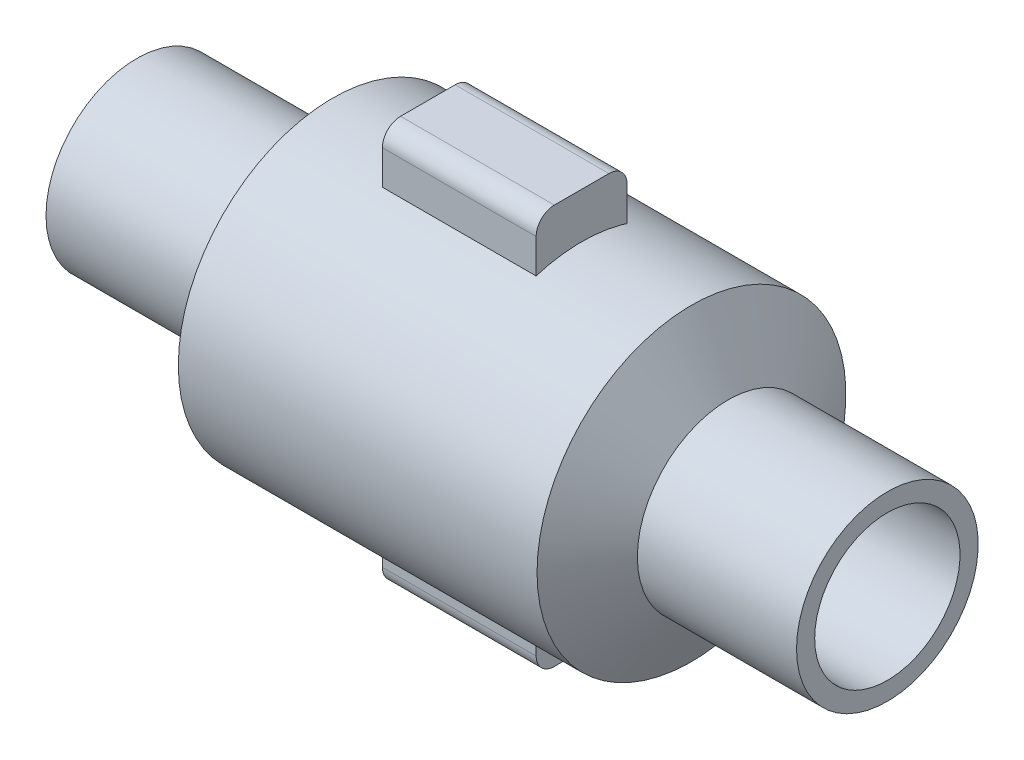
SolidWorks part; units mm, degrees
ref_plane "Front Plane" through (0, 0, 0) normal (0, 0, 1) x (1, 0, 0)
ref_plane "Top Plane" through (0, 0, 0) normal (0, 1, 0) x (1, 0, 0)
ref_plane "Right Plane" through (0, 0, 0) normal (1, 0, 0) x (0, 0, -1)
sketch "Sketch1" plane through (0, 0, 0) normal (0, 0, 1) x (1, 0, 0)
  line L0 (0, 160) -> (0, 200)
  line L1 (0, 200) -> (350.52, 200)
  line L2 (350.52, 200) -> (431.349, 340)
  line L3 (431.349, 340) -> (1221.289, 340)
  line L4 (1221.289, 340) -> (1302.1181, 200)
  line L5 (1302.1181, 200) -> (1652.6381, 200)
  line L6 (1652.6381, 200) -> (1652.6381, 160)
  line L8 (39.8559, 160) -> (350.52, 160)
  line L10 (428.809, 300) -> (1218.749, 300)
  line L12 (1302.1181, 160) -> (1626.6188, 160)
  line L15 (1626.6188, 160) -> (1652.6381, 160)
  line L19 (0, 160) -> (39.8559, 160)
  line L20 (350.52, 160) -> (428.809, 300)
  line L21 (1218.749, 300) -> (1302.1181, 160)
  line L22 (0, 0) -> (1652.6381, 0)
  dimension "D1" = 350.52
  dimension "D2" = 350.52
  dimension "D3" = 789.94
  dimension "D4" = 140
  dimension "D6" = 140
  dimension "D7" = 120
  dimension "D8" = 120
  dimension "D9" = 40
  dimension "D10" = 350.52
  dimension "D11" = 40
  dimension "D12" = 40
  dimension "D13" = 789.94
  dimension "D14" = 787.4
  dimension "D15" = 350.52
revolve "Revolve1" add sketch "Sketch1" angle 360 about L22
ref_plane "Plane1" through (0, 340, 0) normal (0, 1, 0) x (1, 0, 0)
sketch "Sketch3" plane through (0, 340, 0) normal (0, 1, 0) x (1, 0, 0)
  line L1 (640.8521, 100.0933) -> (979.4029, 100.0933)
  line L3 (640.8521, 100.0933) -> (640.8521, -100.0933)
  line L4 (640.8521, -100.0933) -> (979.4029, -100.0933)
  line L5 (979.4029, 100.0933) -> (979.4029, -100.0933)
extrude "Boss-Extrude1" add sketch "Sketch3" along normal blind 100 and the other way blind 40 separate body
fillet "Fillet1" radius 40 2 edges at (810.1275, 440, -100.0933) (810.1275, 440, 100.0933)
ref_plane "Plane2" through (0, -340, 0) normal (0, -1, 0) x (-1, 0, 0)
sketch "Sketch5" plane through (0, -340, 0) normal (0, -1, 0) x (-1, 0, 0)
  line L1 (-979.4029, 100.0933) -> (-640.8521, 100.0933)
  line L2 (-979.4029, 100.0933) -> (-979.4029, -100.0933)
  line L3 (-979.4029, -100.0933) -> (-640.8521, -100.0933)
  line L4 (-640.8521, 100.0933) -> (-640.8521, -100.0933)
extrude "Boss-Extrude2" add sketch "Sketch5" along normal blind 100 and the other way blind 40 separate body
fillet "Fillet2" radius 40 2 edges at (810.1275, -440, 100.0933) (810.1275, -440, -100.0933)
